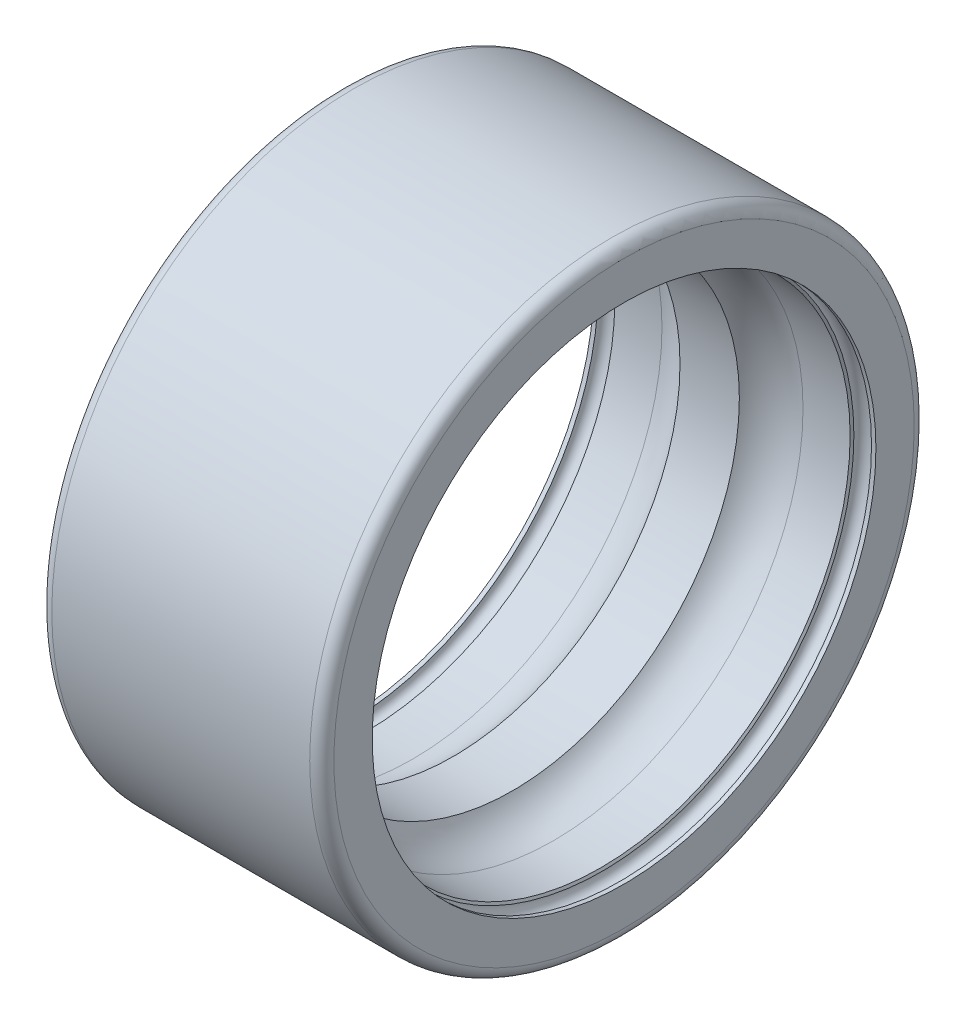
SolidWorks part; units mm, degrees
ref_plane "Front Plane" through (0, 0, 0) normal (0, 0, 1) x (1, 0, 0)
ref_plane "Top Plane" through (0, 0, 0) normal (0, 1, 0) x (1, 0, 0)
ref_plane "Right Plane" through (0, 0, 0) normal (1, 0, 0) x (0, 0, -1)
ref_plane "Plane1" through (0, 0, 0) normal (0, 1, 0) x (-1, 0, 0)
sketch "Sketch1" plane through (0, 0, 0) normal (0, 1, 0) x (-1, 0, 0)
  line L0 (0, -12.5) -> (-0.2188, -12.5)
  line L1 (-1.0938, -12.5) -> (-1.1619, -12.382)
  line L2 (-1.1619, -12.382) -> (-3.5, -12.382)
  line L3 (-5.5277, -11.25) -> (-8.4723, -11.25)
  line L4 (-10.5, -12.382) -> (-12.8381, -12.382)
  line L5 (-12.8381, -12.382) -> (-12.9062, -12.5)
  line L6 (-13.7812, -12.5) -> (-14, -12.5)
  line L7 (-14, -12.5) -> (-14, -14.4)
  line L8 (-13.4, -15) -> (-0.6, -15)
  line L9 (0, -14.4) -> (0, -12.5)
  line L10 (-14, 0) -> (0, 0) construction
  arc A0 (-0.2188, -12.5) -> (-1.0938, -12.5) centre (-0.6562, -12.5) cw
  arc A1 (-3.5, -12.382) -> (-5.5277, -11.25) centre (-3.5, -10) cw
  arc A2 (-8.4723, -11.25) -> (-10.5, -12.382) centre (-10.5, -10) cw
  arc A3 (-12.9062, -12.5) -> (-13.7812, -12.5) centre (-13.3438, -12.5) cw
  arc A4 (-14, -14.4) -> (-13.4, -15) centre (-13.4, -14.4) ccw
  arc A5 (-0.6, -15) -> (0, -14.4) centre (-0.6, -14.4) ccw
revolve "Revolve1" add sketch "Sketch1" angle 360 about L10
